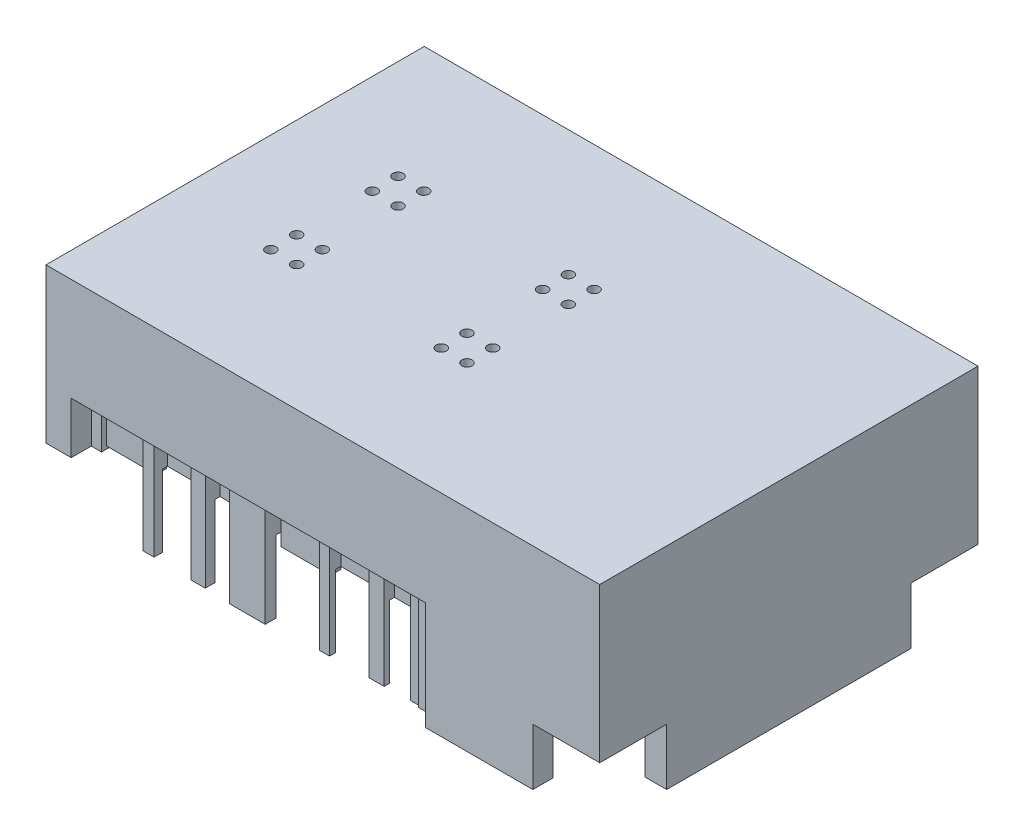
SolidWorks part; units mm, degrees
ref_plane "Front Plane" through (0, 0, 0) normal (0, 0, 1) x (1, 0, 0)
ref_plane "Top Plane" through (0, 0, 0) normal (0, 1, 0) x (1, 0, 0)
ref_plane "Right Plane" through (0, 0, 0) normal (1, 0, 0) x (0, 0, -1)
sketch "Base" plane through (0, 0, 0) normal (0, 1, 0) x (1, 0, 0)
  line L1 (0, 0) -> (107.6, 0)
  line L2 (0, 0) -> (0, 73.5)
  line L3 (0, 73.5) -> (107.6, 73.5)
  line L4 (107.6, 0) -> (107.6, 73.5)
  dimension "D1" = 107.6
  dimension "D2" = 73.5
extrude "Base Extrude" add sketch "Base" along normal blind 10 contours L2 L1 L4 L3
sketch "Sketch2" plane through (0, 0, 0) normal (0, -1, 0) x (1, 0, 0)
  line L6 (0, -73.5) -> (107.6, -73.5) construction
  line L7 (4.9, -73.5) -> (94.6, -73.5)
  line L8 (4.9, -73.5) -> (4.9, -68.6)
  line L9 (4.9, -68.6) -> (94.6, -68.6)
  line L10 (94.6, -73.5) -> (94.6, -68.6)
  line L11 (107.6, 0) -> (107.6, -73.5) construction
  line L12 (0, 0) -> (0, -73.5) construction
  line L13 (0, 0) -> (107.6, 0) construction
  line L14 (4.9, 0) -> (94.6, 0)
  line L15 (4.9, 0) -> (4.9, -4.9)
  line L16 (4.9, -4.9) -> (94.6, -4.9)
  line L17 (94.6, 0) -> (94.6, -4.9)
  dimension "D1" = 13
  dimension "D2" = 4.9
  dimension "D3" = 4.9
  dimension "D4" = 13
  dimension "D5" = 4.9
  dimension "D6" = 4.9
extrude "Side Cut" cut sketch "Sketch2" against normal through all contours L15 L14 L17 L16 | L8 L7 L10 L9
sketch "Sketch3" plane through (0, 0, 0) normal (0, -1, 0) x (-1, 0, 0)
  line L0 (-107.6, 0) -> (-107.6, 73.5) construction
  line L1 (-107.6, 13) -> (-102.6, 13)
  line L2 (-107.6, 13) -> (-107.6, 60.5)
  line L3 (-107.6, 60.5) -> (-102.6, 60.5)
  line L4 (-102.6, 13) -> (-102.6, 60.5)
  line L5 (-94.6, 0) -> (-107.6, 0) construction
  line L6 (-94.6, 73.5) -> (-107.6, 73.5) construction
  dimension "D1" = 13
  dimension "D2" = 13
  dimension "D3" = 5
extrude "Front Extrude" add sketch "Sketch3" along normal blind 11
sketch "Sketch4" plane through (0, 10, 0) normal (0, 1, 0) x (1, 0, 0)
  line L0 (4.9, 4.9) -> (94.6, 4.9) construction
  line L1 (94.6, 0) -> (67.7, 0)
  line L2 (94.6, 0) -> (94.6, 4.9)
  line L3 (94.6, 4.9) -> (67.7, 4.9)
  line L4 (67.7, 0) -> (67.7, 4.9)
  line L5 (4.9, 68.6) -> (94.6, 68.6) construction
  line L6 (62.8, 4.9) -> (59.9, 4.9)
  line L7 (62.8, 4.9) -> (62.8, 0.1)
  line L8 (62.8, 0.1) -> (59.9, 0.1)
  line L9 (59.9, 4.9) -> (59.9, 0.1)
  line L10 (50.4, 4.9) -> (52.4, 4.9)
  line L11 (50.4, 4.9) -> (50.4, 0.1)
  line L12 (50.4, 0.1) -> (52.4, 0.1)
  line L13 (52.4, 4.9) -> (52.4, 0.1)
  line L14 (40.8, 4.9) -> (33.9, 4.9)
  line L15 (40.8, 4.9) -> (40.8, 0.1)
  line L16 (40.8, 0.1) -> (33.9, 0.1)
  line L17 (33.9, 4.9) -> (33.9, 0.1)
  line L18 (26.1, 4.9) -> (28.9, 4.9)
  line L19 (26.1, 4.9) -> (26.1, 0.1)
  line L20 (26.1, 0.1) -> (28.9, 0.1)
  line L21 (28.9, 4.9) -> (28.9, 0.1)
  line L22 (16.5, 4.9) -> (18.7, 4.9)
  line L23 (16.5, 4.9) -> (16.5, 0.1)
  line L24 (16.5, 0.1) -> (18.7, 0.1)
  line L25 (18.7, 4.9) -> (18.7, 0.1)
  line L30 (94.6, 68.6) -> (67.2, 68.6)
  line L31 (94.6, 68.6) -> (94.6, 73.4)
  line L32 (94.6, 73.4) -> (67.2, 73.4)
  line L33 (67.2, 68.6) -> (67.2, 73.4)
  line L34 (57.4, 68.6) -> (55.1, 68.6)
  line L35 (57.4, 68.6) -> (57.4, 73.4)
  line L36 (57.4, 73.4) -> (55.1, 73.4)
  line L37 (55.1, 68.6) -> (55.1, 73.4)
  line L39 (47.6, 68.6) -> (44.6, 68.6)
  line L40 (47.6, 68.6) -> (47.6, 73.4)
  line L41 (47.6, 73.4) -> (44.6, 73.4)
  line L42 (44.6, 68.6) -> (44.6, 73.4)
  line L43 (39.6, 68.6) -> (33.1, 68.6)
  line L44 (39.6, 68.6) -> (39.6, 73.4)
  line L45 (39.6, 73.4) -> (33.1, 73.4)
  line L46 (33.1, 68.6) -> (33.1, 73.4)
  line L47 (23.5, 68.6) -> (21.5, 68.6)
  line L48 (23.5, 68.6) -> (23.5, 73.4)
  line L49 (23.5, 73.4) -> (21.5, 73.4)
  line L50 (21.5, 68.6) -> (21.5, 73.4)
  line L51 (14, 68.6) -> (11.8, 68.6)
  line L52 (14, 68.6) -> (14, 73.4)
  line L53 (14, 73.4) -> (11.8, 73.4)
  line L54 (11.8, 68.6) -> (11.8, 73.4)
  line L55 (4.9, 4.9) -> (6.9, 4.9)
  line L56 (4.9, 4.9) -> (4.9, 0.1)
  line L57 (4.9, 0.1) -> (6.9, 0.1)
  line L58 (6.9, 4.9) -> (6.9, 0.1)
  line L59 (4.9, 68.6) -> (6.9, 68.6)
  line L60 (4.9, 68.6) -> (4.9, 73.4)
  line L61 (4.9, 73.4) -> (6.9, 73.4)
  line L62 (6.9, 68.6) -> (6.9, 73.4)
  dimension "D1" = 26.9
  dimension "D2" = 4.9
  dimension "D3" = 2.9
  dimension "D4" = 7.5
  dimension "D5" = 2
  dimension "D6" = 9.6
  dimension "D7" = 6.9
  dimension "D8" = 4.8
  dimension "D9" = 4.8
  dimension "D10" = 4.8
  dimension "D11" = 4.8
  dimension "D12" = 2.8
  dimension "D13" = 5
  dimension "D14" = 7.4
  dimension "D15" = 2.2
  dimension "D16" = 4.8
  dimension "D17" = 2
  dimension "D18" = 4.8
  dimension "D19" = 27.4
  dimension "D20" = 9.8
  dimension "D21" = 2.3
  dimension "D22" = 4.8
  dimension "D23" = 7.5
  dimension "D24" = 4.8
  dimension "D25" = 3
  dimension "D26" = 6.5
  dimension "D27" = 5
  dimension "D28" = 9.6
  dimension "D29" = 4.8
  dimension "D30" = 2
  dimension "D31" = 7.5
  dimension "D32" = 2.2
  dimension "D33" = 4.8
  dimension "D34" = 4.8
  dimension "D35" = 4.8
  dimension "D36" = 4.8
  dimension "D37" = 2
extrude "Terminal Extrudes" add sketch "Sketch4" against normal blind 21
sketch "Sketch5" plane through (0, 10, 0) normal (0, 1, 0) x (1, 0, 0)
  line L0 (0, 36.75) -> (107.6, 36.75) construction
  line L1 (0, 0) -> (0, 73.5) construction
  line L2 (107.6, 0) -> (107.6, 73.5) construction
  line L3 (38.35, 68.6) -> (38.35, 0.1) construction
  line L4 (16.8, 41.6) -> (26.8, 41.6)
  line L5 (16.8, 41.6) -> (16.8, 51.6)
  line L6 (16.8, 51.6) -> (26.8, 51.6)
  line L7 (26.8, 41.6) -> (26.8, 51.6)
  line L8 (23.5, 68.6) -> (33.1, 68.6) construction
  line L9 (39.6, 68.6) -> (44.6, 68.6) construction
  line L10 (33.9, 0.1) -> (40.8, 0.1) construction
  line L11 (59.9, 51.6) -> (49.9, 51.6)
  line L12 (49.9, 41.6) -> (49.9, 51.6)
  line L13 (59.9, 41.6) -> (49.9, 41.6)
  line L14 (59.9, 41.6) -> (59.9, 51.6)
  line L15 (59.9, 31.9) -> (59.9, 21.9)
  line L16 (59.9, 31.9) -> (49.9, 31.9)
  line L17 (49.9, 31.9) -> (49.9, 21.9)
  line L18 (59.9, 21.9) -> (49.9, 21.9)
  line L19 (16.8, 21.9) -> (26.8, 21.9)
  line L20 (26.8, 31.9) -> (26.8, 21.9)
  line L21 (16.8, 31.9) -> (26.8, 31.9)
  line L22 (16.8, 31.9) -> (16.8, 21.9)
  line L23 (16.8, 46.6) -> (26.8, 46.6) construction
  line L24 (21.8, 51.6) -> (21.8, 41.6) construction
  circle A1 centre (24.3, 49.1) radius 1
  circle A2 centre (24.3, 44.1) radius 1
  circle A3 centre (19.3, 44.1) radius 1
  circle A4 centre (19.3, 49.1) radius 1
  circle A5 centre (52.4, 49.1) radius 1
  circle A6 centre (52.4, 44.1) radius 1
  circle A7 centre (57.4, 44.1) radius 1
  circle A8 centre (57.4, 49.1) radius 1
  circle A9 centre (57.4, 29.4) radius 1
  circle A10 centre (52.4, 29.4) radius 1
  circle A11 centre (57.4, 24.4) radius 1
  circle A12 centre (52.4, 24.4) radius 1
  circle A13 centre (24.3, 29.4) radius 1
  circle A14 centre (24.3, 24.4) radius 1
  circle A15 centre (19.3, 24.4) radius 1
  circle A16 centre (19.3, 29.4) radius 1
  dimension "D6" = 2.5
  dimension "D8" = 2
  dimension "D1" = 16.8
  dimension "D2" = 17
  dimension "D3" = 10
  dimension "D4" = 10
  dimension "D5" = 11.55
  dimension "D7" = 2.5
extrude "Fiber Holes" cut sketch "Sketch5" against normal through all both and the other way through all contours A4 | A1 | A3 | A2 | A13 | A15 | A14 | A6 | A5 | A8 | A10 | A9 | A12 | A11 | A7 | A16
sketch "Sketch6" plane through (0, 0, 0) normal (0, -1, 0) x (1, 0, 0)
  line L0 (0, 0) -> (0, -73.5) construction
  line L1 (1.2, -52.8) -> (4.7, -52.8)
  line L2 (1.2, -52.8) -> (1.2, -59.8)
  line L3 (1.2, -59.8) -> (4.7, -59.8)
  line L4 (4.7, -52.8) -> (4.7, -59.8)
  line L5 (0, -73.5) -> (4.9, -73.5) construction
  line L6 (0, 0) -> (4.9, 0) construction
  line L7 (1.2, -13.7) -> (4.7, -13.7)
  line L8 (1.2, -13.7) -> (1.2, -20.7)
  line L9 (1.2, -20.7) -> (4.7, -20.7)
  line L10 (4.7, -13.7) -> (4.7, -20.7)
  dimension "D1" = 4.7
  dimension "D2" = 3.5
  dimension "D3" = 7
  dimension "D4" = 13.7
  dimension "D5" = 13.7
  dimension "D6" = 3.5
  dimension "D7" = 7
  dimension "D8" = 4.7
extrude "Female Pin Connectors" cut sketch "Sketch6" against normal blind 2.5
sketch "Sketch8" plane through (0, 10, 0) normal (0, 1, 0) x (1, 0, 0)
  line L0 (6.9, 68.6) -> (11.8, 68.6) construction
  line L1 (4.9, 73.5) -> (4.7, 73.5)
  line L2 (4.9, 73.5) -> (4.9, 68.6)
  line L3 (4.9, 68.6) -> (4.7, 68.6)
  line L4 (4.7, 73.5) -> (4.7, 68.6)
  dimension "D1" = 0.2
sketch "Sketch10" plane through (0, -11, 0) normal (0, -1, 0) x (-1, 0, 0)
  line L1 (-94.6, 68.6) -> (-4.9, 68.6)
  line L2 (-94.6, 68.6) -> (-94.6, 69.6)
  line L3 (-94.6, 69.6) -> (-4.9, 69.6)
  line L4 (-4.9, 68.6) -> (-4.9, 69.6)
  line L6 (-94.6, 4.9) -> (-4.9, 4.9)
  line L7 (-94.6, 4.9) -> (-94.6, 3.9)
  line L8 (-94.6, 3.9) -> (-4.9, 3.9)
  line L9 (-4.9, 4.9) -> (-4.9, 3.9)
  dimension "D1" = 1
  dimension "D2" = 1
extrude "Side Altercation" cut sketch "Sketch10" against normal up to surface (11 mm away) up to face at (2.95, 0, -56.3)
sketch "Sketch11" plane through (0, -11, 0) normal (0, -1, 0) x (-1, 0, 0)
  line L0 (-102.6, 60.5) -> (-107.6, 60.5) construction
  line L1 (-102.6, 13) -> (-103.4, 13)
  line L2 (-102.6, 13) -> (-102.6, 60.5)
  line L3 (-102.6, 60.5) -> (-103.4, 60.5)
  line L4 (-103.4, 13) -> (-103.4, 60.5)
  dimension "D1" = 0.8
extrude "Front Altercation" cut sketch "Sketch11" against normal up to surface (11 mm away) up to face at (43.4716, 0, -37.297)
sketch "Sketch13" plane through (0, 0, 0) normal (0, -1, 0) x (1, 0, 0)
  line L1 (6.9, -3.9) -> (103.4, -3.9)
  line L2 (6.9, -3.9) -> (6.9, -69.6)
  line L3 (6.9, -69.6) -> (103.4, -69.6)
  line L4 (103.4, -3.9) -> (103.4, -69.6)
extrude "Master Depth Altercation" cut sketch "Sketch13" against normal blind 3
sketch "Sketch14" plane through (0, 3, 0) normal (0, -1, 0) x (1, 0, 0)
  line L0 (6.9, -69.6) -> (6.9, -3.9) construction
  line L1 (6.9, -9.9) -> (98.4, -9.9)
  line L2 (6.9, -9.9) -> (6.9, -63.6)
  line L3 (6.9, -63.6) -> (98.4, -63.6)
  line L4 (98.4, -9.9) -> (98.4, -63.6)
  line L5 (4.9, -4.9) -> (94.6, -4.9) construction
  line L6 (4.9, -68.6) -> (94.6, -68.6) construction
  line L7 (103.4, -60.5) -> (103.4, -13) construction
  dimension "D1" = 5
  dimension "D2" = 5
  dimension "D3" = 5
extrude "Cut Weight" cut sketch "Sketch14" against normal blind 4
sketch "Sketch15" plane through (0, 3, 0) normal (0, -1, 0) x (-1, 0, 0)
  line L1 (-6.9, 4.9) -> (-16.5, 4.9)
  line L2 (-6.9, 4.9) -> (-6.9, 6.9)
  line L3 (-6.9, 6.9) -> (-16.5, 6.9)
  line L4 (-16.5, 4.9) -> (-16.5, 6.9)
  line L5 (-40.8, 4.9) -> (-50.4, 4.9)
  line L6 (-40.8, 4.9) -> (-40.8, 6.9)
  line L7 (-40.8, 6.9) -> (-50.4, 6.9)
  line L8 (-50.4, 4.9) -> (-50.4, 6.9)
  dimension "D1" = 2
  dimension "D2" = 2
extrude "Cover Gold Plate (Right Side) " add sketch "Sketch15" along normal blind 2.5
sketch "Sketch16" plane through (0, 3, 0) normal (0, -1, 0) x (1, 0, 0)
  line L1 (33.1, -68.6) -> (23.5, -68.6)
  line L2 (33.1, -68.6) -> (33.1, -66.6)
  line L3 (33.1, -66.6) -> (23.5, -66.6)
  line L4 (23.5, -68.6) -> (23.5, -66.6)
  line L5 (67.2, -68.6) -> (57.4, -68.6)
  line L6 (67.2, -68.6) -> (67.2, -66.6)
  line L7 (67.2, -66.6) -> (57.4, -66.6)
  line L8 (57.4, -68.6) -> (57.4, -66.6)
  dimension "D1" = 2
  dimension "D2" = 2
extrude "Gold Plate Adjustment" add sketch "Sketch16" along normal blind 2
sketch "Sketch17" plane through (0, -11, 0) normal (0, -1, 0) x (1, 0, 0)
  line L1 (11.8, -69.6) -> (23.5, -69.6)
  line L2 (11.8, -69.6) -> (11.8, -68.1)
  line L3 (11.8, -68.1) -> (23.5, -68.1)
  line L4 (23.5, -69.6) -> (23.5, -68.1)
  line L6 (23.5, -69.6) -> (23.5, -73.4) construction
  line L8 (33.1, -69.6) -> (57.4, -69.6)
  line L9 (33.1, -69.6) -> (33.1, -68.87)
  line L10 (33.1, -68.87) -> (57.4, -68.87)
  line L11 (57.4, -69.6) -> (57.4, -68.87)
  dimension "D1" = 1.5
  dimension "D2" = 0.73
extrude "Right Side Extrude" add sketch "Sketch17" against normal up to surface (14 mm away)
sketch "Sketch18" plane through (0, -11, 0) normal (0, -1, 0) x (1, 0, 0)
  line L0 (23.5, -68.1) -> (11.8, -68.1) construction
  line L1 (39.6, -69.6) -> (44.6, -69.6)
  line L2 (39.6, -69.6) -> (39.6, -68.87)
  line L3 (39.6, -68.87) -> (44.6, -68.87)
  line L4 (44.6, -69.6) -> (44.6, -68.87)
  line L5 (47.6, -69.6) -> (55.1, -69.6)
  line L6 (47.6, -69.6) -> (47.6, -68.87)
  line L7 (47.6, -68.87) -> (55.1, -68.87)
  line L8 (55.1, -69.6) -> (55.1, -68.87)
  line L10 (14, -69.6) -> (14, -68.1)
  line L11 (14, -68.1) -> (21.5, -68.1)
  line L12 (21.5, -69.6) -> (21.5, -68.1)
  line L13 (14, -69.6) -> (21.5, -69.6) construction
  line L14 (23.5, -68.1) -> (23.5, -73.4) construction
  line L15 (11.8, -73.4) -> (23.5, -73.4)
  line L16 (11.8, -73.4) -> (11.8, -69.5)
  line L17 (11.8, -69.5) -> (14, -69.5)
  line L18 (23.5, -73.4) -> (23.5, -69.5)
  line L19 (57.4, -68.87) -> (57.4, -73.4) construction
  line L20 (44.6, -73.4) -> (57.4, -73.4)
  line L21 (44.6, -73.4) -> (44.6, -71.4)
  line L22 (44.6, -71.4) -> (57.4, -71.4)
  line L23 (57.4, -73.4) -> (57.4, -71.4)
  line L24 (21.5, -69.5) -> (23.5, -69.5)
  line L25 (14, -73.4) -> (21.5, -73.4)
  dimension "D1" = 3.9
  dimension "D2" = 2
extrude "Right Side Adjustment" cut sketch "Sketch18" against normal through all
sketch "Sketch19" plane through (0, -11, 0) normal (0, -1, 0) x (1, 0, 0)
  line L0 (6.9, -69.6) -> (6.9, -3.9) construction
  line L1 (6.9, -69.5) -> (4.9, -69.5)
  line L2 (6.9, -69.5) -> (6.9, -68.1)
  line L3 (6.9, -68.1) -> (4.9, -68.1)
  line L4 (4.9, -69.5) -> (4.9, -68.1)
extrude "Right Corner Extrude" add sketch "Sketch19" against normal up to surface (11 mm away) up to face at (2.95, 0, -56.3)
sketch "Sketch21" plane through (0, -11, 0) normal (0, -1, 0) x (1, 0, 0)
  line L1 (6.9, -69.6) -> (0, -69.6)
  line L2 (6.9, -69.6) -> (6.9, -73.5)
  line L3 (6.9, -73.5) -> (0, -73.5)
  line L4 (0, -69.6) -> (0, -73.5)
extrude "Right Corner Adj" cut sketch "Sketch21" against normal through all
sketch "Sketch22" plane through (0, -11, 0) normal (0, -1, 0) x (1, 0, 0)
  line L5 (18.7, -0.1) -> (18.7, -3.9) construction
  line L6 (16.5, -0.1) -> (18.7, -0.1)
  line L7 (16.5, -0.1) -> (16.5, -1.9)
  line L8 (16.5, -1.9) -> (18.7, -1.9)
  line L9 (18.7, -0.1) -> (18.7, -1.9)
  line L10 (28.9, -0.1) -> (28.9, -3.9) construction
  line L11 (26.1, -0.1) -> (28.9, -0.1)
  line L12 (26.1, -0.1) -> (26.1, -1.65)
  line L13 (26.1, -1.65) -> (28.9, -1.65)
  line L14 (28.9, -0.1) -> (28.9, -1.65)
  line L15 (52.4, -0.1) -> (52.4, -3.9) construction
  line L16 (50.4, -0.1) -> (52.4, -0.1)
  line L17 (50.4, -0.1) -> (50.4, -2.3)
  line L18 (50.4, -2.3) -> (52.4, -2.3)
  line L19 (52.4, -0.1) -> (52.4, -2.3)
  line L20 (62.8, -0.1) -> (62.8, -3.9) construction
  line L21 (59.9, -0.1) -> (62.8, -0.1)
  line L22 (59.9, -0.1) -> (59.9, -2.5)
  line L23 (59.9, -2.5) -> (62.8, -2.5)
  line L24 (62.8, -0.1) -> (62.8, -2.5)
  dimension "D1" = 1.8
  dimension "D2" = 1.55
  dimension "D3" = 2.2
  dimension "D4" = 2.4
extrude "Left Side Adjustment" cut sketch "Sketch22" against normal through all
sketch "Sketch23" plane through (0, 0, 0) normal (0, 0, 1) x (1, 0, 0)
  line L0 (67.7, 10) -> (107.6, 10) construction
  line L1 (67.7, -11) -> (73.7, -11)
  line L2 (67.7, -11) -> (67.7, 10)
  line L3 (67.7, 10) -> (73.7, 10)
  line L4 (73.7, -11) -> (73.7, 10)
  dimension "D1" = 6
extrude "Side Panel Adjust" cut sketch "Sketch23" against normal blind 2.7
sketch "Sketch24" plane through (0, 10, 0) normal (0, 1, 0) x (1, 0, 0)
  line L0 (107.6, 36.75) -> (0, 36.75) construction
  line L1 (107.6, 0) -> (107.6, 73.5) construction
  line L2 (0, 0) -> (0, 69.6) construction
  line L3 (38.35, 65.459) -> (38.35, 12.8449) construction
  circle A0 centre (19.3, 49.1) radius 2
  circle A1 centre (24.3, 49.1) radius 2
  circle A2 centre (19.3, 44.1) radius 2
  circle A3 centre (24.3, 44.1) radius 1
  circle A4 centre (24.3, 44.1) radius 2
  circle A5 centre (24.3, 49.1) radius 1
  circle A6 centre (19.3, 49.1) radius 1
  circle A7 centre (19.3, 44.1) radius 1
  circle A8 centre (52.4, 29.4) radius 1 construction
  circle A9 centre (24.3, 29.4) radius 1 construction
  circle A10 centre (52.4, 49.1) radius 1
  circle A11 centre (52.4, 49.1) radius 2
  circle A12 centre (52.4, 44.1) radius 1
  circle A13 centre (52.4, 44.1) radius 2
  circle A14 centre (57.4, 44.1) radius 1
  circle A15 centre (57.4, 44.1) radius 2
  circle A16 centre (57.4, 49.1) radius 1
  circle A17 centre (57.4, 49.1) radius 2
  circle A18 centre (57.4, 29.4) radius 1
  circle A19 centre (57.4, 29.4) radius 2
  circle A20 centre (57.4, 24.4) radius 1
  circle A21 centre (57.4, 24.4) radius 2
  circle A22 centre (52.4, 24.4) radius 1
  circle A23 centre (52.4, 24.4) radius 2
  circle A24 centre (52.4, 29.4) radius 1
  circle A25 centre (52.4, 29.4) radius 2
  circle A26 centre (24.3, 24.4) radius 1
  circle A27 centre (24.3, 24.4) radius 2
  circle A28 centre (24.3, 29.4) radius 1
  circle A29 centre (24.3, 29.4) radius 2
  circle A30 centre (19.3, 29.4) radius 1
  circle A31 centre (19.3, 29.4) radius 2
  circle A32 centre (19.3, 24.4) radius 2
  circle A33 centre (19.3, 24.4) radius 1
  dimension "D1" = 2
  dimension "D2" = 4
  dimension "D3" = 4
  dimension "D4" = 2
  dimension "D5" = 2
  dimension "D6" = 4
  dimension "D7" = 2
  dimension "D8" = 4
extrude "Pipes" add sketch "Sketch24" along normal blind 25
sketch "Sketch25" plane through (0, 10, 0) normal (0, 1, 0) x (1, 0, 0)
  line L5 (0, 0) -> (107.6, 0)
  line L6 (0, 0) -> (0, 73.5)
  line L18 (0, 73.5) -> (107.6, 73.5)
  line L19 (107.6, 0) -> (107.6, 73.5)
extrude "Extra Space Created" add sketch "Sketch25" along normal blind 20
sketch "Sketch26" plane through (0, 7, 0) normal (0, -1, 0) x (1, 0, 0)
  line L1 (6.9, -9.9) -> (98.4, -9.9)
  line L2 (6.9, -9.9) -> (6.9, -63.6)
  line L3 (6.9, -63.6) -> (98.4, -63.6)
  line L4 (98.4, -9.9) -> (98.4, -63.6)
  circle A0 centre (19.3, -24.4) radius 1
  circle A1 centre (24.3, -24.4) radius 1
  circle A2 centre (19.3, -29.4) radius 1
  circle A3 centre (24.3, -29.4) radius 1
  circle A4 centre (52.4, -24.4) radius 1
  circle A5 centre (57.4, -24.4) radius 1
  circle A6 centre (52.4, -29.4) radius 1
  circle A7 centre (57.4, -29.4) radius 1
  circle A8 centre (19.3, -44.1) radius 1
  circle A9 centre (24.3, -44.1) radius 1
  circle A10 centre (52.4, -49.1) radius 1
  circle A11 centre (52.4, -44.1) radius 1
  circle A12 centre (57.4, -44.1) radius 1
  circle A13 centre (57.4, -49.1) radius 1
  circle A14 centre (24.3, -49.1) radius 1
  circle A15 centre (19.3, -49.1) radius 1
extrude "Extra Space" cut sketch "Sketch26" against normal blind 20
sketch "Sketch27" plane through (0, 35, 0) normal (0, 1, 0) x (1, 0, 0)
  circle A0 centre (52.4, 29.4) radius 1
  circle A1 centre (52.4, 24.4) radius 1
  circle A2 centre (57.4, 24.4) radius 1
  circle A3 centre (57.4, 29.4) radius 1
  circle A4 centre (57.4, 44.1) radius 1
  circle A5 centre (57.4, 49.1) radius 1
  circle A6 centre (52.4, 49.1) radius 1
  circle A7 centre (24.3, 49.1) radius 1
  circle A8 centre (24.3, 44.1) radius 1
  circle A9 centre (19.3, 49.1) radius 1
  circle A10 centre (19.3, 44.1) radius 1
  circle A11 centre (19.3, 29.4) radius 1
  circle A12 centre (24.3, 29.4) radius 1
  circle A13 centre (24.3, 24.4) radius 1
  circle A14 centre (19.3, 24.4) radius 1
  circle A15 centre (52.4, 44.1) radius 1
sketch "Sketch29" plane through (0, 27, 0) normal (0, -1, 0) x (1, 0, 0)
  line L0 (14.0106, -36.75) -> (66.2851, -36.75) construction
  line L1 (38.35, -53.0758) -> (38.35, -18.5715) construction
  line L2 (21.8, -33.2471) -> (21.8, -20.3764) construction
  line L3 (28.6516, -26.9) -> (14.6219, -26.9) construction
  circle A0 centre (19.3, -44.1) radius 1 construction
  circle A1 centre (19.3, -29.4) radius 1 construction
  circle A2 centre (52.4, -29.4) radius 1 construction
  circle A3 centre (24.3, -29.4) radius 1 construction
  circle A4 centre (24.3, -29.4) radius 1
  circle A5 centre (24.3, -29.4) radius 2
  circle A6 centre (19.3, -24.4) radius 1 construction
  circle A7 centre (24.3, -24.4) radius 1 construction
  circle A8 centre (19.3, -29.4) radius 2
  circle A9 centre (19.3, -29.4) radius 1
  circle A10 centre (19.3, -24.4) radius 1
  circle A11 centre (19.3, -24.4) radius 2
  circle A12 centre (24.3, -24.4) radius 2
  circle A13 centre (24.3, -24.4) radius 1
  circle A14 centre (57.4, -29.4) radius 1
  circle A15 centre (57.4, -29.4) radius 2
  circle A16 centre (57.4, -24.4) radius 1
  circle A17 centre (57.4, -24.4) radius 2
  circle A18 centre (52.4, -24.4) radius 1
  circle A19 centre (52.4, -24.4) radius 2
  circle A20 centre (52.4, -29.4) radius 2
  circle A21 centre (52.4, -29.4) radius 1
  circle A22 centre (19.3, -49.1) radius 1
  circle A23 centre (19.3, -49.1) radius 2
  circle A24 centre (24.3, -49.1) radius 1
  circle A25 centre (24.3, -49.1) radius 2
  circle A26 centre (19.3, -44.1) radius 1
  circle A27 centre (19.3, -44.1) radius 2
  circle A28 centre (24.3, -44.1) radius 1
  circle A29 centre (24.3, -44.1) radius 2
  circle A30 centre (57.4, -44.1) radius 2
  circle A31 centre (57.4, -44.1) radius 1
  circle A32 centre (57.4, -49.1) radius 2
  circle A33 centre (57.4, -49.1) radius 1
  circle A34 centre (52.4, -49.1) radius 1
  circle A35 centre (52.4, -49.1) radius 2
  circle A36 centre (52.4, -44.1) radius 1
  circle A37 centre (52.4, -44.1) radius 2
  dimension "D1" = 4
extrude "Boss-Extrude7" add sketch "Sketch29" along normal blind 10
sketch "Sketch30" plane through (0, 0, 0) normal (-1, 0, 0) x (0, 0, 1)
  line L1 (-73.5, 30) -> (0, 30)
  line L2 (-73.5, 30) -> (-73.5, 50)
  line L3 (-73.5, 50) -> (0, 50)
  line L4 (0, 30) -> (0, 50)
  dimension "D1" = 20
extrude "Cut-Extrude10" cut sketch "Sketch30" against normal blind 100
sketch "Sketch31" plane through (0, 10, 0) normal (0, -1, 0) x (-1, 0, 0)
  circle A0 centre (-57.4, 49.1) radius 1
  circle A1 centre (-52.4, 49.1) radius 1
  circle A2 centre (-57.4, 44.1) radius 1
  circle A3 centre (-52.4, 44.1) radius 1
  circle A4 centre (-24.3, 49.1) radius 1
  circle A5 centre (-19.3, 49.1) radius 1
  circle A6 centre (-24.3, 44.1) radius 1
  circle A7 centre (-19.3, 44.1) radius 1
  circle A8 centre (-57.4, 29.4) radius 1
  circle A9 centre (-52.4, 29.4) radius 1
  circle A10 centre (-57.4, 24.4) radius 1
  circle A11 centre (-52.4, 24.4) radius 1
  circle A12 centre (-24.3, 29.4) radius 1
  circle A13 centre (-19.3, 29.4) radius 1
  circle A14 centre (-24.3, 24.4) radius 1
  circle A15 centre (-19.3, 24.4) radius 1
extrude "Cut-Extrude11" cut sketch "Sketch31" against normal through all
sketch "Sketch32" plane through (0, -11, 0) normal (0, -1, 0) x (1, 0, 0)
  line L0 (44.6, -71.4) -> (44.6, -68.87) construction
  line L1 (57.4, -71.4) -> (44.6, -71.4)
  line L2 (57.4, -71.4) -> (57.4, -71)
  line L3 (57.4, -71) -> (44.6, -71)
  line L4 (44.6, -71.4) -> (44.6, -71)
  dimension "D1" = 0.4
extrude "Cut-Extrude12" cut sketch "Sketch32" against normal up to surface (21 mm away) up to face at (36.9214, 10, -70.2)
sketch "Sketch33" plane through (0, -11, 0) normal (0, -1, 0) x (1, 0, 0)
  line L0 (33.1, -73.4) -> (33.1, -68.87) construction
  line L1 (39.6, -73.4) -> (33.1, -73.4)
  line L2 (39.6, -73.4) -> (39.6, -71.1)
  line L3 (39.6, -71.1) -> (33.1, -71.1)
  line L4 (33.1, -73.4) -> (33.1, -71.1)
  dimension "D1" = 2.3
extrude "Cut-Extrude13" cut sketch "Sketch33" against normal up to surface (21 mm away) up to face at (36.9214, 10, -70.1429)
sketch "Sketch34" plane through (0, -11, 0) normal (0, -1, 0) x (-1, 0, 0)
  line L1 (-6.9, 69.5) -> (-4.9, 69.5)
  line L2 (-6.9, 69.5) -> (-6.9, 68.1)
  line L3 (-6.9, 68.1) -> (-4.9, 68.1)
  line L4 (-4.9, 69.5) -> (-4.9, 68.1)
extrude "To Left Bottom" cut sketch "Sketch34" against normal up to surface (21 mm away) up to face at (36.9214, 10, -69.9786)
sketch "Sketch35" plane through (0, -11, 0) normal (0, -1, 0) x (1, 0, 0)
  line L1 (6.9, -3.9) -> (4.9, -3.9)
  line L2 (6.9, -3.9) -> (6.9, -0.1)
  line L3 (6.9, -0.1) -> (4.9, -0.1)
  line L4 (4.9, -3.9) -> (4.9, -0.1)
extrude "To Right Bottom" cut sketch "Sketch35" against normal up to surface (21 mm away) up to face at (38.8286, 10, -2.9036)
sketch "Sketch36" plane through (0, -11, 0) normal (0, -1, 0) x (1, 0, 0)
  line L1 (94.6, -3.9) -> (67.7, -3.9)
  line L2 (94.6, -3.9) -> (94.6, -4.5)
  line L3 (94.6, -4.5) -> (67.7, -4.5)
  line L4 (67.7, -3.9) -> (67.7, -4.5)
  line L5 (62.8, -3.9) -> (59.9, -3.9)
  line L6 (62.8, -3.9) -> (62.8, -4.5)
  line L7 (62.8, -4.5) -> (59.9, -4.5)
  line L8 (59.9, -3.9) -> (59.9, -4.5)
  line L9 (52.4, -3.9) -> (50.4, -3.9)
  line L10 (52.4, -3.9) -> (52.4, -4.5)
  line L11 (52.4, -4.5) -> (50.4, -4.5)
  line L12 (50.4, -3.9) -> (50.4, -4.5)
  line L13 (40.8, -3.9) -> (33.9, -3.9)
  line L14 (40.8, -3.9) -> (40.8, -4.5)
  line L15 (40.8, -4.5) -> (33.9, -4.5)
  line L16 (33.9, -3.9) -> (33.9, -4.5)
  line L17 (28.9, -3.9) -> (26.1, -3.9)
  line L18 (28.9, -3.9) -> (28.9, -4.5)
  line L19 (28.9, -4.5) -> (26.1, -4.5)
  line L20 (26.1, -3.9) -> (26.1, -4.5)
  line L21 (18.7, -3.9) -> (16.5, -3.9)
  line L22 (18.7, -3.9) -> (18.7, -4.5)
  line L23 (18.7, -4.5) -> (16.5, -4.5)
  line L24 (16.5, -3.9) -> (16.5, -4.5)
  dimension "D1" = 0.6
  dimension "D2" = 0.6
  dimension "D3" = 0.6
  dimension "D4" = 0.6
  dimension "D5" = 0.6
  dimension "D6" = 0.6
sketch "Sketch37" plane through (0, -11, 0) normal (0, -1, 0) x (-1, 0, 0)
  line L1 (-16.5, 1.9) -> (-18.7, 1.9)
  line L2 (-16.5, 1.9) -> (-16.5, 2.3)
  line L3 (-16.5, 2.3) -> (-18.7, 2.3)
  line L4 (-18.7, 1.9) -> (-18.7, 2.3)
  line L5 (-26.1, 1.65) -> (-28.9, 1.65)
  line L6 (-26.1, 1.65) -> (-26.1, 2.05)
  line L7 (-26.1, 2.05) -> (-28.9, 2.05)
  line L8 (-28.9, 1.65) -> (-28.9, 2.05)
  line L9 (-33.9, 0.1) -> (-40.8, 0.1)
  line L10 (-33.9, 0.1) -> (-33.9, 1.8)
  line L11 (-33.9, 1.8) -> (-40.8, 1.8)
  line L12 (-40.8, 0.1) -> (-40.8, 1.8)
  line L13 (-50.4, 2.3) -> (-52.4, 2.3)
  line L14 (-50.4, 2.3) -> (-50.4, 2.7)
  line L15 (-50.4, 2.7) -> (-52.4, 2.7)
  line L16 (-52.4, 2.3) -> (-52.4, 2.7)
  line L17 (-59.9, 2.5) -> (-62.8, 2.5)
  line L18 (-59.9, 2.5) -> (-59.9, 2.9)
  line L19 (-59.9, 2.9) -> (-62.8, 2.9)
  line L20 (-62.8, 2.5) -> (-62.8, 2.9)
  line L21 (-67.7, 2.7) -> (-69.6409, 2.7)
  line L22 (-67.7, 2.7) -> (-67.7, 3.1)
  line L23 (-67.7, 3.1) -> (-69.6409, 3.1)
  line L24 (-69.6409, 2.7) -> (-69.6409, 3.1)
  dimension "D1" = 0.4
  dimension "D2" = 0.4
  dimension "D3" = 1.7
  dimension "D4" = 0.4
  dimension "D5" = 0.4
  dimension "D6" = 0.4
extrude "Cut-Extrude17" cut sketch "Sketch37" against normal up to surface (21 mm away) up to face at (33.0437, 10, -69.8312)
sketch "Sketch38" plane through (0, 17, 0) normal (0, -1, 0) x (1, 0, 0)
  line L0 (6.9, -9.9) -> (6.9, -63.6) construction
  line L1 (16.9, -53.6) -> (63.4, -53.6)
  line L2 (16.9, -53.6) -> (16.9, -19.9)
  line L3 (16.9, -19.9) -> (63.4, -19.9)
  line L4 (63.4, -53.6) -> (63.4, -19.9)
  line L5 (98.4, -9.9) -> (6.9, -9.9) construction
  line L6 (98.4, -63.6) -> (98.4, -9.9) construction
  line L7 (6.9, -63.6) -> (98.4, -63.6) construction
  dimension "D1" = 10
  dimension "D2" = 10
  dimension "D3" = 35
  dimension "D4" = 10
extrude "Cut-Extrude18" cut sketch "Sketch38" against normal blind 6
